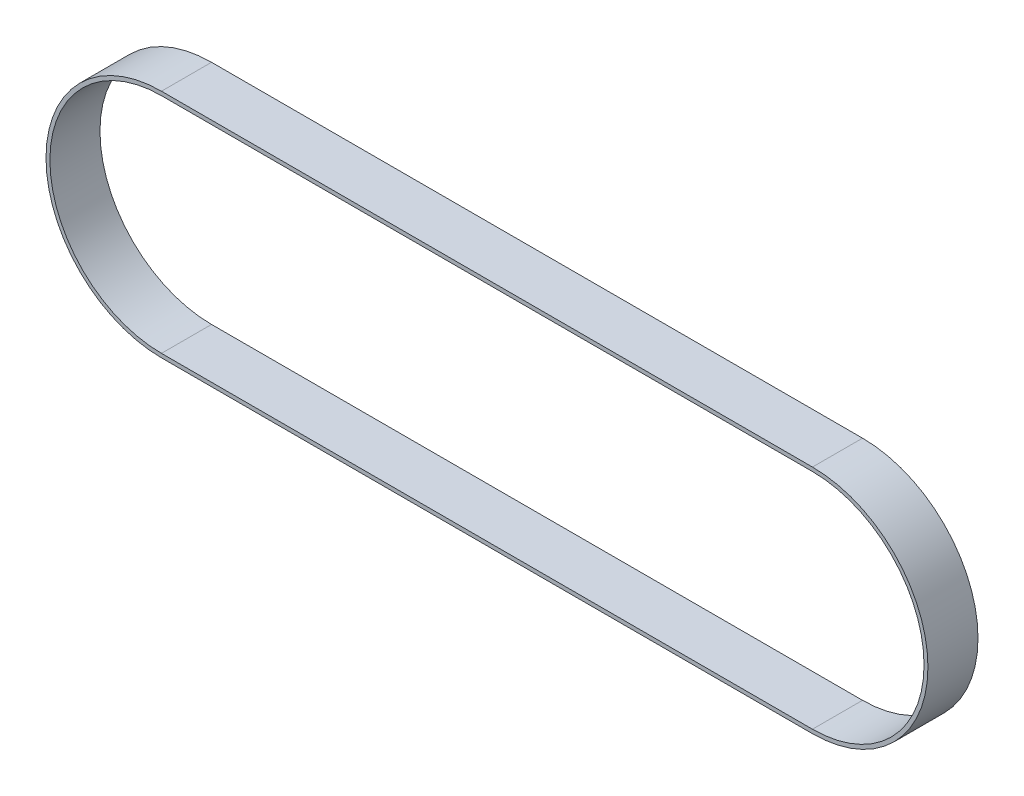
SolidWorks part; units mm, degrees
ref_plane "Front Plane" through (0, 0, 0) normal (0, 0, 1) x (1, 0, 0)
ref_plane "Top Plane" through (0, 0, 0) normal (0, 1, 0) x (1, 0, 0)
ref_plane "Right Plane" through (0, 0, 0) normal (1, 0, 0) x (0, 0, -1)
sketch "Sketch1" plane through (0, 0, 0) normal (0, 0, 1) x (1, 0, 0)
  line L0 (0, 33.4264) -> (195.0466, 33.4264)
  line L1 (0, -33.4264) -> (195.0466, -33.4264)
  line L2 (0, 34.5948) -> (195.0466, 34.5948)
  line L3 (0, -34.5948) -> (195.0466, -34.5948)
  arc A0 (0, 33.4264) -> (0, -33.4264) centre (0, 0) ccw
  arc A1 (195.0466, -33.4264) -> (195.0466, 33.4264) centre (195.0466, 0) ccw
  arc A2 (195.0466, -34.5948) -> (195.0466, 34.5948) centre (195.0466, 0) ccw
  arc A3 (0, 34.5948) -> (0, -34.5948) centre (0, 0) ccw
  dimension "D1" = 66.8528
  dimension "D2" = 195.0466
  dimension "D3" = 1.1684
extrude "Boss-Extrude1" add sketch "Sketch1" along normal blind 15
